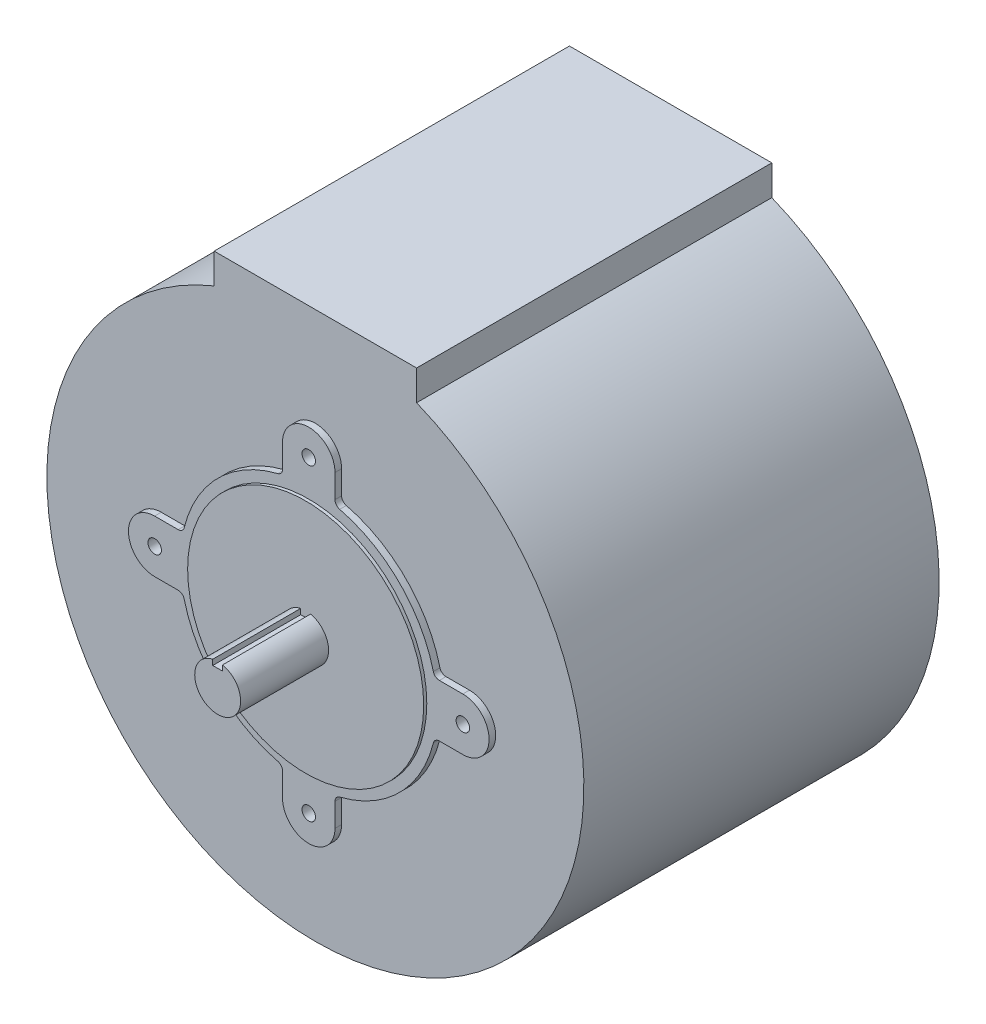
SolidWorks part; units mm, degrees
ref_plane "Front Plane" through (0, 0, 0) normal (0, 0, 1) x (1, 0, 0)
ref_plane "Top Plane" through (0, 0, 0) normal (0, 1, 0) x (1, 0, 0)
ref_plane "Right Plane" through (0, 0, 0) normal (1, 0, 0) x (0, 0, -1)
sketch "Sketch1" plane through (0, 0, 0) normal (0, 0, 1) x (1, 0, 0)
  circle A0 centre (0, 0) radius 130
  dimension "D1" = 260
extrude "Boss-Extrude1" add sketch "Sketch1" against normal blind 172
sketch "Sketch2" plane through (0, 0, 0) normal (0, 0, 1) x (1, 0, 0)
  line L0 (-74.6, 12.7) -> (-63.23, 12.7)
  line L1 (-74.6, -12.7) -> (-63.23, -12.7)
  line L2 (-12.7, -74.6) -> (-12.7, -63.23)
  line L3 (12.7, -74.6) -> (12.7, -63.23)
  line L4 (74.6, -12.7) -> (63.23, -12.7)
  line L5 (74.6, 12.7) -> (63.23, 12.7)
  line L6 (12.7, 74.6) -> (12.7, 63.23)
  line L7 (-12.7, 74.6) -> (-12.7, 63.23)
  circle A0 centre (0, 0) radius 74.6 construction
  arc A1 (12.6539, 73.519) -> (-12.6539, 73.519) centre (0, 74.6) ccw
  arc A2 (73.519, -12.6539) -> (73.519, 12.6539) centre (74.6, 0) ccw
  arc A3 (-12.6539, -73.519) -> (12.6539, -73.519) centre (0, -74.6) ccw
  arc A4 (-73.519, 12.6539) -> (-73.519, -12.6539) centre (-74.6, 0) ccw
  arc A5 (-14.9771, 60.3184) -> (-60.3184, 14.9771) centre (0, 0) ccw
  arc A6 (-60.3184, -14.9771) -> (-14.9771, -60.3184) centre (0, 0) ccw
  arc A7 (14.9771, -60.3184) -> (60.3184, -14.9771) centre (0, 0) ccw
  arc A8 (60.3184, 14.9771) -> (14.9771, 60.3184) centre (0, 0) ccw
  arc A9 (12.7, 63.23) -> (14.9771, 60.3184) centre (15.7, 63.23) ccw
  arc A10 (63.23, 12.7) -> (60.3184, 14.9771) centre (63.23, 15.7) cw
  arc A11 (63.23, -12.7) -> (60.3184, -14.9771) centre (63.23, -15.7) ccw
  arc A12 (12.7, -63.23) -> (14.9771, -60.3184) centre (15.7, -63.23) cw
  arc A13 (-12.7, -63.23) -> (-14.9771, -60.3184) centre (-15.7, -63.23) ccw
  arc A14 (-63.23, -12.7) -> (-60.3184, -14.9771) centre (-63.23, -15.7) cw
  arc A15 (-63.23, 12.7) -> (-60.3184, 14.9771) centre (-63.23, 15.7) ccw
  arc A16 (-12.7, 63.23) -> (-14.9771, 60.3184) centre (-15.7, 63.23) cw
  point P35 (60.8386, 12.7)
  point P38 (60.8386, -12.7)
  point P41 (12.7, -60.8386)
  point P44 (-12.7, -60.8386)
  point P47 (-60.8386, -12.7)
  dimension "D1" = 149.2
  dimension "D2" = 124.3
  dimension "D3" = 25.4
  dimension "D4" = 3
extrude "Boss-Extrude2" add sketch "Sketch2" along normal blind 3.2
sketch "Sketch3" plane through (0, 0, 3.2) normal (0, 0, 1) x (1, 0, 0)
  circle A0 centre (0, 0) radius 57.15
  dimension "D1" = 114.3
extrude "Boss-Extrude3" add sketch "Sketch3" along normal blind 1.5
hole_wizard "5/16-18 Tapped Hole1" positions "Sketch5" profile "Sketch4" tap size "5/16-18" standard "ANSI Inch"
sketch "Sketch5" plane through (0, 0, 3.2) normal (0, 0, 1) x (1, 0, 0)
  circle A0 centre (0, 0) radius 74.6 construction
  point P0 (-74.6, 0)
  point P4 (0, 74.6)
  point P12 (74.6, 0)
  point P14 (0, -74.6)
sketch "Sketch4" plane through (-74.6, 0, 3.2) normal (1, 0, 0) x (0, -1, 0)
  line L0 (0, 0) -> (0, 22.0702)
  line L1 (0, 22.0702) -> (3.2639, 20.1091)
  line L2 (3.2639, 20.1091) -> (3.2639, 0)
  line L5 (3.2639, 0) -> (0, 0)
  line L10 (0, 22.0702) -> (-3.2639, 20.1091) construction
  line L11 (0, -6.35) -> (0, 107.95) construction
  dimension "Tap Drill Dia." = 6.5278
  dimension "Tap Drill Depth" = 20.1091
  dimension "Drill Angle" = 118
cosmetic thread "Hole Thread1" parameters "D1"=15.88, "D2"=7.9375
cosmetic thread "Hole Thread2" parameters "D1"=15.88, "D2"=7.9375
cosmetic thread "Hole Thread3" parameters "D1"=15.88, "D2"=7.9375
cosmetic thread "Hole Thread4" parameters "D1"=15.88, "D2"=7.9375
sketch "Sketch6" plane through (0, 0, 0) normal (0, 0, 1) x (1, 0, 0)
  line L1 (-49, 135) -> (49, 135)
  line L2 (-49, 135) -> (-49, 87.3)
  line L3 (-49, 87.3) -> (49, 87.3)
  line L4 (49, 135) -> (49, 87.3)
  line L5 (-49, 135) -> (49, 87.3) construction
  line L6 (-49, 87.3) -> (49, 135) construction
  circle A0 centre (0, 0) radius 130 construction
  arc A1 (12.6539, 73.519) -> (-12.6539, 73.519) centre (0, 74.6) ccw construction
  point P0 (0, 130)
  point P7 (0, 87.3)
  dimension "D1" = 135
  dimension "D2" = 98
extrude "Boss-Extrude4" add sketch "Sketch6" against normal up to surface (172 mm away) up to face at (130, 0, -172)
sketch "Sketch7" plane through (0, 0, 4.7) normal (0, 0, 1) x (1, 0, 0)
  line L2 (-2.39, 10.855) -> (-2.39, 8.205)
  line L3 (-2.39, 8.205) -> (2.39, 8.205)
  line L4 (2.39, 10.855) -> (2.39, 8.205)
  arc A0 (-2.39, 10.855) -> (2.39, 10.855) centre (0, 0) ccw
  point P7 (0, 8.205)
  dimension "D1" = 22.23
  dimension "D2" = 2.65
  dimension "D3" = 4.78
extrude "Boss-Extrude5" add sketch "Sketch7" along normal blind 42.6
